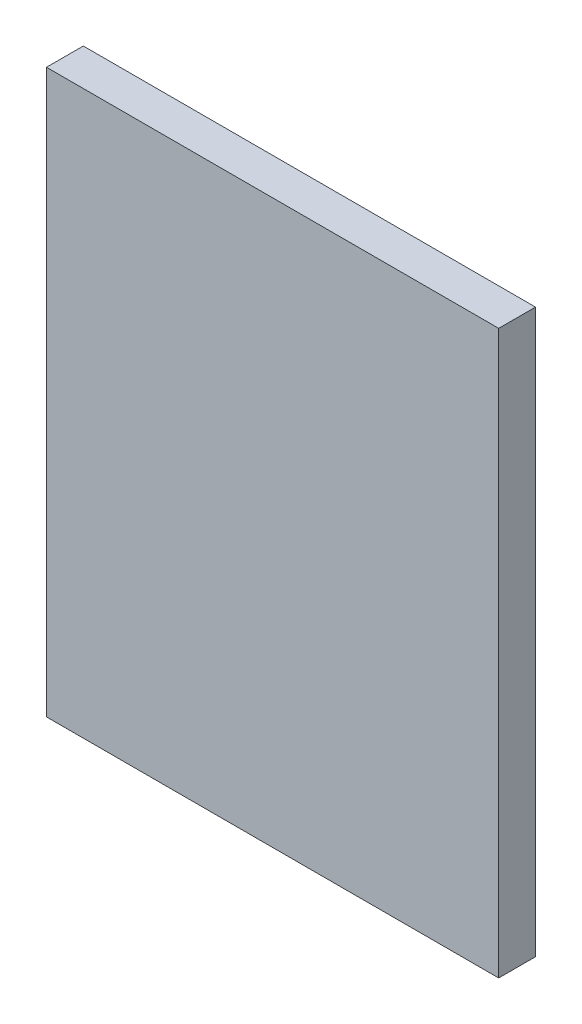
SolidWorks part; units mm, degrees
ref_plane "Ön Düzlem" through (0, 0, 0) normal (0, 0, 1) x (1, 0, 0)
ref_plane "Üst Düzlem" through (0, 0, 0) normal (0, 1, 0) x (1, 0, 0)
ref_plane "Sağ Düzlem" through (0, 0, 0) normal (1, 0, 0) x (0, 0, -1)
sketch "Çizim1" plane through (0, 0, 0) normal (0, 0, 1) x (1, 0, 0)
  line L1 (-69.0101, 504.3771) -> (360.9899, 504.3771)
  line L2 (-69.0101, 504.3771) -> (-69.0101, -30.6229)
  line L3 (-69.0101, -30.6229) -> (360.9899, -30.6229)
  line L4 (360.9899, 504.3771) -> (360.9899, -30.6229)
  dimension "D1" = 535
  dimension "D2" = 430
  dimension "D3" = 535
  dimension "D4" = 430
extrude "Yükseklik-Ekstrüzyon1" add sketch "Çizim1" along normal blind 35
sketch "Çizim2" plane through (0, 0, 35) normal (0, 0, 1) x (1, 0, 0)
  line L0 (-29.0029, 504.3771) -> (-29.0029, -30.6229)
  line L1 (360.9899, 504.3771) -> (-69.0101, 504.3771) construction
  line L2 (-69.0101, -30.6229) -> (360.9899, -30.6229) construction
  line L3 (6.8271, 504.3771) -> (6.8271, -30.6229)
  line L4 (42.6571, 504.3771) -> (42.6571, -30.6229)
  line L5 (78.4871, 504.3771) -> (78.4871, -30.6229)
  line L6 (114.3171, 504.3771) -> (114.3171, -30.6229)
  line L7 (150.1471, 504.3771) -> (150.1471, -30.6229)
  line L8 (185.9771, 504.3771) -> (185.9771, -30.6229)
  line L9 (221.8071, 504.3771) -> (221.8071, -30.6229)
  line L10 (257.6371, 504.3771) -> (257.6371, -30.6229)
  line L11 (293.4671, 504.3771) -> (293.4671, -30.6229)
  line L12 (329.2971, 504.3771) -> (329.2971, -30.6229)
  line L13 (-69.0101, 8.4205) -> (360.9899, 8.4205)
  line L14 (365.1271, 504.3771) -> (365.1271, -30.6229)
  line L15 (-69.0101, 504.3771) -> (-69.0101, -30.6229) construction
  line L16 (360.9899, -30.6229) -> (360.9899, 504.3771) construction
  line L17 (-59.0101, 8.4205) -> (370.9899, 8.4205)
  line L18 (-69.0101, 115.7858) -> (360.9899, 115.7858)
  line L19 (-69.0101, 223.151) -> (360.9899, 223.151)
  line L20 (-69.0101, 330.5163) -> (360.9899, 330.5163)
  line L21 (-69.0101, 437.8815) -> (360.9899, 437.8815)
  point P35 (150.1471, 125.3403)
  dimension "D1" = 12
  dimension "D2" = 2
  dimension "D3" = 5
